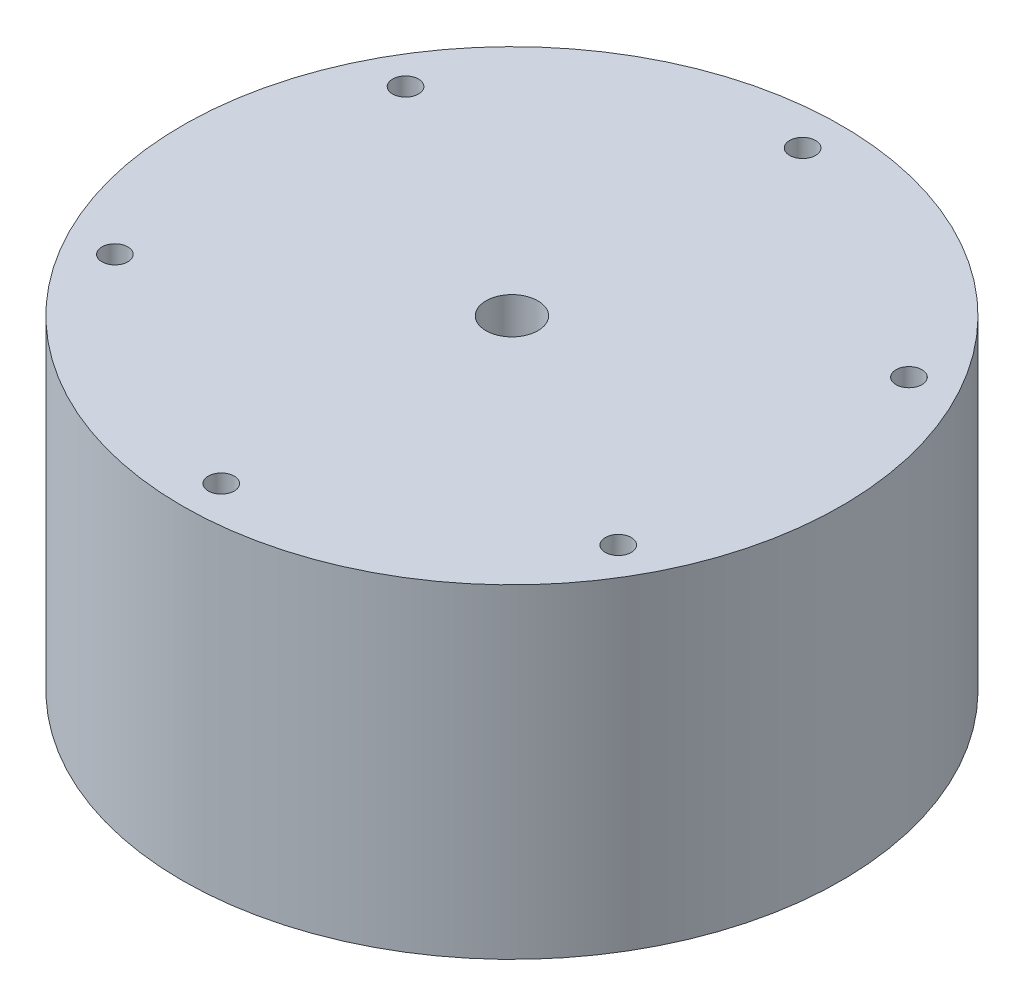
SolidWorks part; units mm, degrees
ref_plane "Front Plane" through (0, 0, 0) normal (0, 0, 1) x (1, 0, 0)
ref_plane "Top Plane" through (0, 0, 0) normal (0, 1, 0) x (1, 0, 0)
ref_plane "Right Plane" through (0, 0, 0) normal (1, 0, 0) x (0, 0, -1)
sketch "Sketch1" plane through (0, 0, 0) normal (0, 1, 0) x (1, 0, 0)
  circle A0 centre (0, 0) radius 50.8
  dimension "D1" = 101.6
extrude "Boss-Extrude1" add sketch "Sketch1" along normal blind 50
sketch "Sketch2" plane through (0, 0, 0) normal (0, -1, 0) x (1, 0, 0)
  circle A0 centre (0, 0) radius 38.1
  circle A1 centre (0, 0) radius 36.5
  dimension "D1" = 76.2
  dimension "D2" = 1.6
sketch "Sketch3" plane through (0, 0, 0) normal (0, 0, 1) x (1, 0, 0)
  line L3 (0, 0) -> (38.1, 0)
  line L4 (38.1, 0) -> (38.1, 2)
  line L5 (38.1, 2) -> (36.5, 2)
  line L6 (36.5, 2) -> (0, 38.5)
  line L7 (0, 38.5) -> (0, 0)
  dimension "D1" = 38.1
  dimension "D2" = 2
  dimension "D3" = 1.6
  dimension "D4" = 135
revolve "Cut-Revolve1" cut sketch "Sketch3" angle 360 about L7
sketch "Sketch4" plane through (0, 50, 0) normal (0, 1, 0) x (1, 0, 0)
  line L0 (0, 0) -> (0, 50.8) construction
  circle A0 centre (0, 0) radius 4
  circle A1 centre (0, 0) radius 50.8 construction
  circle A2 centre (0, 44.8) radius 2
  circle A3 centre (38.7979, 22.4) radius 2
  circle A4 centre (38.7979, -22.4) radius 2
  circle A5 centre (0, -44.8) radius 2
  circle A6 centre (-38.7979, -22.4) radius 2
  circle A7 centre (-38.7979, 22.4) radius 2
  point P20 (0, 0)
  dimension "D1" = 4
  dimension "D2" = 6
  dimension "D3" = 6
extrude "Cut-Extrude2" cut sketch "Sketch4" against normal blind 71
